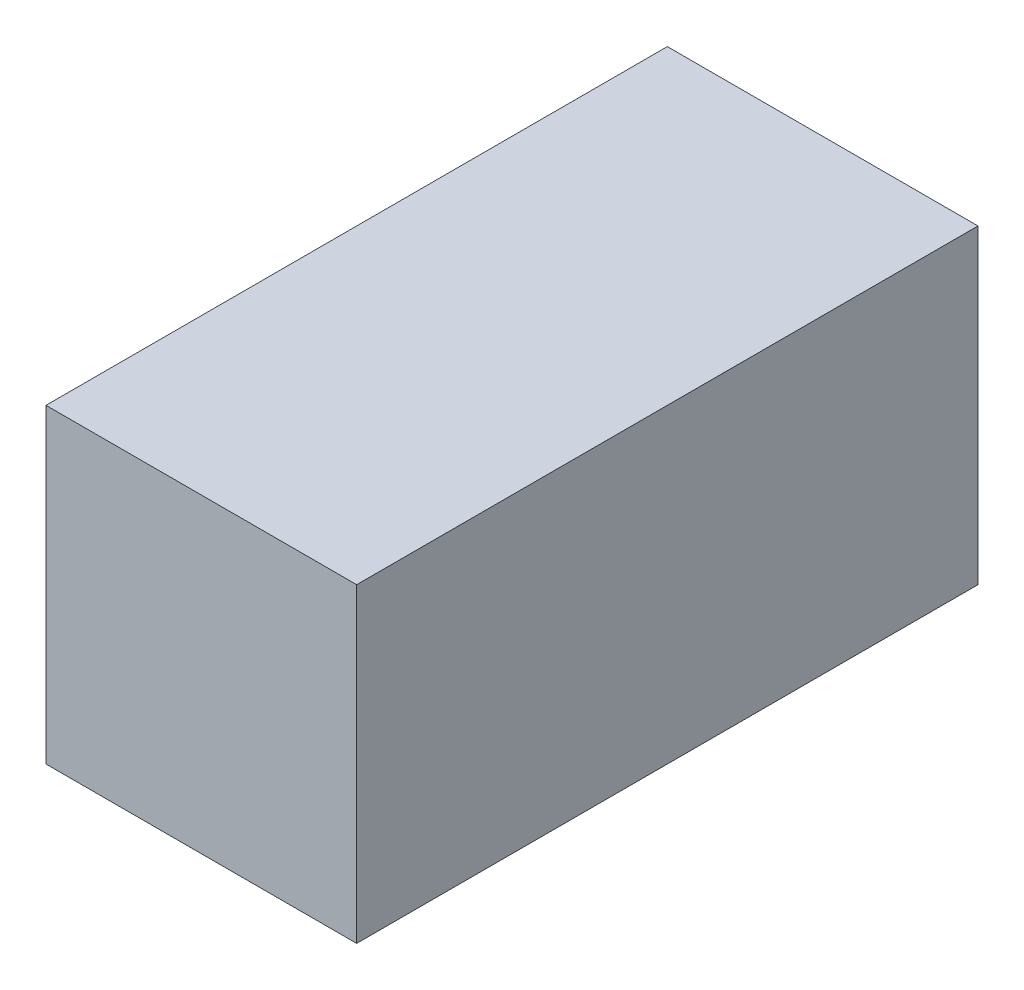
SolidWorks part; units mm, degrees
ref_plane "Front Plane" through (0, 0, 0) normal (0, 0, 1) x (1, 0, 0)
ref_plane "Top Plane" through (0, 0, 0) normal (0, 1, 0) x (1, 0, 0)
ref_plane "Right Plane" through (0, 0, 0) normal (1, 0, 0) x (0, 0, -1)
sketch "Sketch1" plane through (0, 0, 0) normal (0, 0, 1) x (1, 0, 0)
  line L1 (-2.5, -2.5) -> (2.5, -2.5)
  line L2 (-2.5, -2.5) -> (-2.5, 2.5)
  line L3 (-2.5, 2.5) -> (2.5, 2.5)
  line L4 (2.5, -2.5) -> (2.5, 2.5)
  line L5 (-2.5, -2.5) -> (2.5, 2.5) construction
  line L6 (-2.5, 2.5) -> (2.5, -2.5) construction
  point P0 (0, 0)
  dimension "D1" = 5
  dimension "D2" = 5
extrude "Boss-Extrude1" add sketch "Sketch1" along normal blind 10
